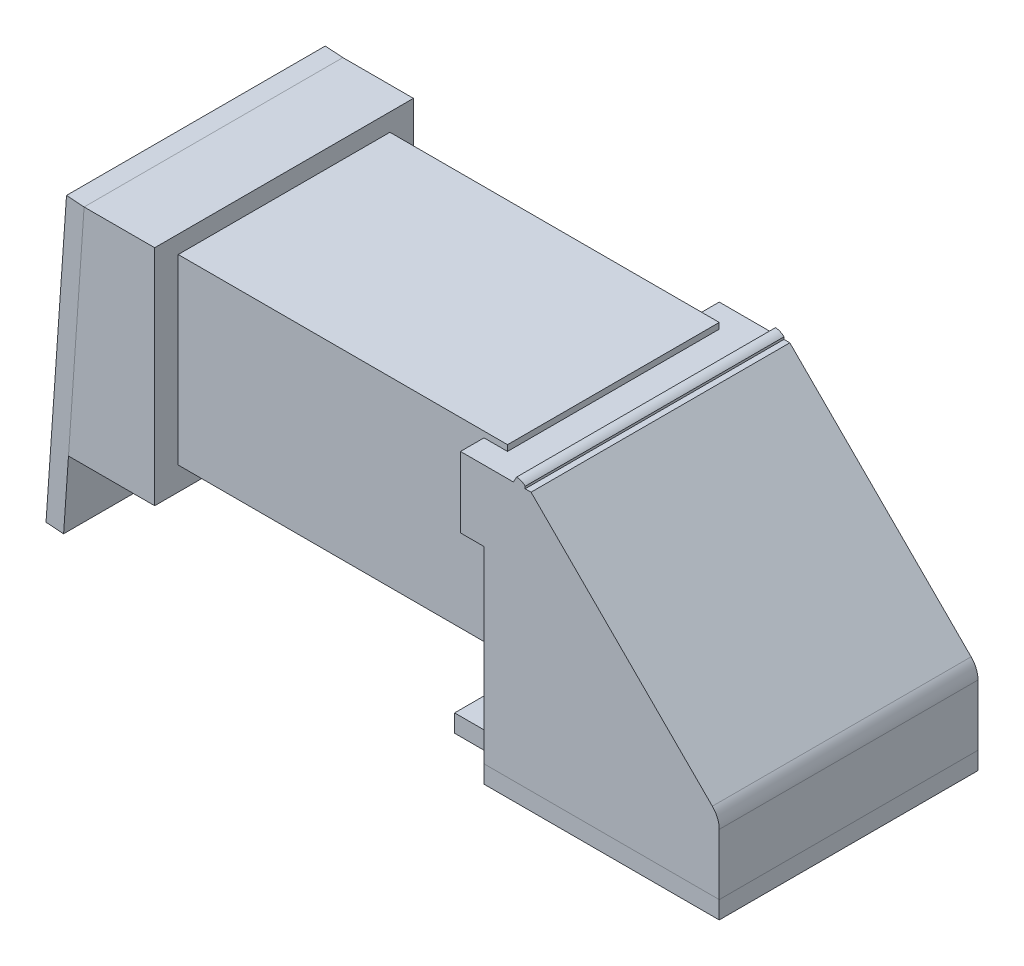
SolidWorks part; units mm, degrees
material "PVC 0.007 plastifié"
ref_plane "Face" through (0, 0, 0) normal (0, 0, 1) x (1, 0, 0)
ref_plane "Dessus" through (0, 0, 0) normal (0, 1, 0) x (1, 0, 0)
ref_plane "Droite" through (0, 0, 0) normal (1, 0, 0) x (0, 0, -1)
sketch "Esquisse2" plane through (0, 0, 0) normal (0, 0, 1) x (1, 0, 0)
  line L0 (-20, 0) -> (0, 0)
  line L2 (-22, 22) -> (-16, 22)
  line L3 (-22, 22) -> (-22, 16)
  line L4 (-22, 16) -> (-20, 16)
  line L5 (-20, 16) -> (-20, 0)
  line L6 (0, 0) -> (0, 6)
  line L7 (-16, 22) -> (0, 6)
  dimension "D1" = 45
  dimension "D2" = 16
  dimension "D3" = 6
  dimension "D4" = 6
  dimension "D5" = 2
  dimension "D6" = 20
extrude "Extrusion1" add sketch "Esquisse2" along normal mid plane 22
sketch "Esquisse3" plane through (-20, 0, 0) normal (-1, 0, 0) x (0, 0, 1)
  line L0 (0, 0) -> (0, 7.2849) construction
  line L1 (-9, 22.5) -> (9, 22.5)
  line L2 (-9, 22.5) -> (-9, 7)
  line L3 (-9, 7) -> (9, 7)
  line L4 (9, 22.5) -> (9, 7)
  line L5 (11, 0) -> (-11, 0) construction
  dimension "D1" = 18
  dimension "D2" = 15.5
  dimension "D3" = 7
extrude "Extrusion2" add sketch "Esquisse3" along normal blind 28
sketch "Esquisse4" plane through (-48, 0, 0) normal (-1, 0, 0) x (0, 0, 1)
  line L0 (0, 0) -> (0, 12.8722) construction
  line L1 (-11, 24) -> (11, 24)
  line L2 (-11, 24) -> (-11, 5)
  line L3 (-11, 5) -> (11, 5)
  line L4 (11, 24) -> (11, 5)
  line L5 (9, 22.5) -> (-9, 22.5) construction
  dimension "D1" = 22
  dimension "D2" = 19
  dimension "D3" = 1.5
extrude "Extrusion3" add sketch "Esquisse4" along normal blind 6
draft "Dépouille1" type of draft neutral plane draft angle 4 faces to draft 1 face at (-54, 14.5, 0) neutral plane through (-54, 24, -11) neutral plane normal (0, 1, 0) parameters "D1"=4
shell "Coque1" thickness 2
sketch "Esquisse6" plane through (-55.4073, 3.8745, 0) normal (-0.9976, 0.0698, 0) x (0, 0, 1)
  line L1 (11, 20.1747) -> (-11, 20.1747)
  line L2 (11, 20.1747) -> (11, -4.8253)
  line L3 (11, -4.8253) -> (-11, -4.8253)
  line L4 (-11, 20.1747) -> (-11, -4.8253)
  dimension "D1" = 22
  dimension "D2" = 25
extrude "Extrusion4" add sketch "Esquisse6" along normal blind 1.5 separate body
sketch "Esquisse7" plane through (0, 0, 0) normal (0, -1, 0) x (1, 0, 0)
  line L0 (0, 0) -> (-10.2378, 0) construction
  line L1 (0, 11) -> (-20, 11)
  line L2 (0, 11) -> (0, -11)
  line L3 (0, -11) -> (-20, -11)
  line L4 (-20, 11) -> (-20, 8.5)
  line L5 (-20, 8.5) -> (-25, 8.5)
  line L7 (-20, -8.5) -> (-25, -8.5)
  line L8 (-25, 8.5) -> (-25, -8.5)
  line L9 (-20, -8.5) -> (-20, -11)
  dimension "D1" = 20
  dimension "D2" = 5
  dimension "D3" = 17
sketch "Esquisse8" plane through (0, 0, -11) normal (0, 0, -1) x (-1, 0, 0)
  line L0 (16.5, 22) -> (16.5, 22.1867)
  line L1 (16, 22) -> (22, 22) construction
  line L2 (22, 22) -> (22, 16) construction
  line L3 (17.227, 22.5) -> (17.5, 22)
  line L4 (17.5, 22) -> (16.5, 22)
  line L5 (20, 22.5) -> (15.8797, 22.5) construction
  arc A1 (17.227, 22.5) -> (16.5, 22.1867) centre (17.227, 21.5) ccw
  dimension "D1" = 1
  dimension "D2" = 1
  dimension "D3" = 4.773
  dimension "D4" = 0.5
extrude "Extrusion7" add sketch "Esquisse8" against normal up to surface (22 mm away) up to face at (-14.2857, 11.7143, 11)
extrude "Extrusion13" add sketch "Esquisse7" along normal blind 1.5 separate body
fillet "Congé1" radius 2 1 edges at (0, 6, 0)
